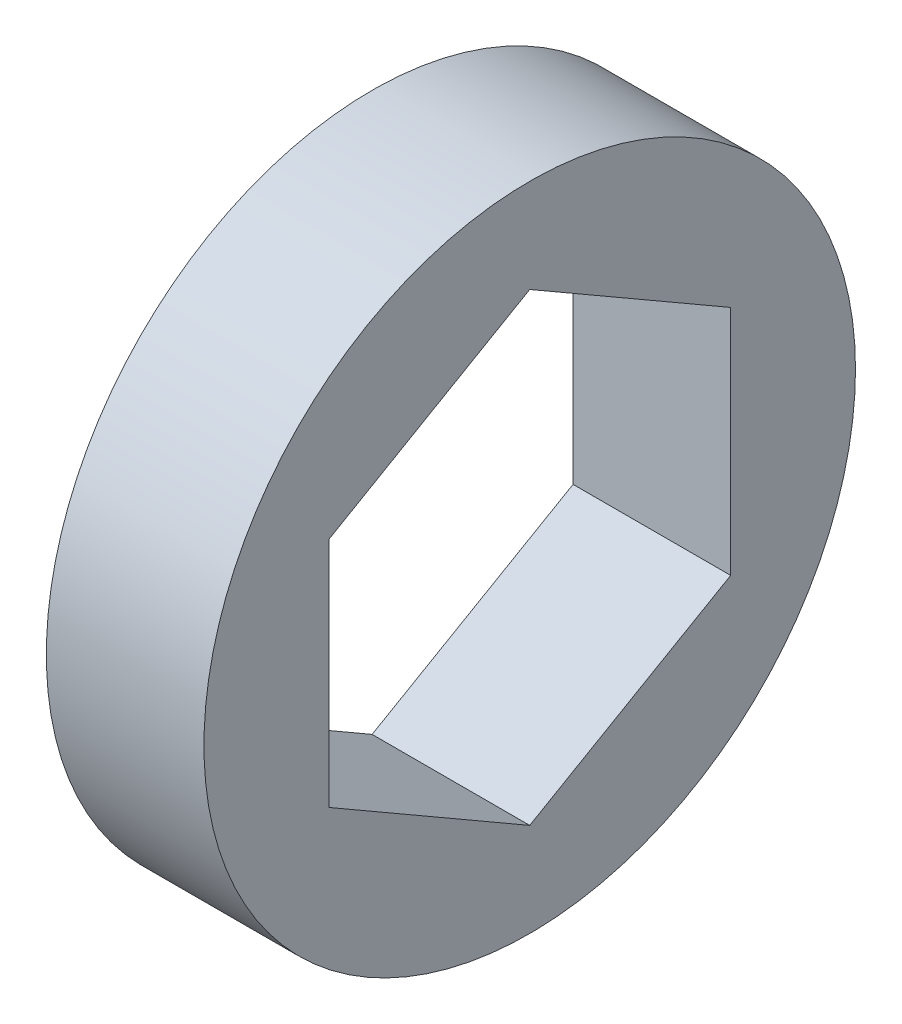
SolidWorks part; units mm, degrees
ref_plane "Front" through (0, 0, 0) normal (0, 0, 1) x (1, 0, 0)
ref_plane "Top" through (0, 0, 0) normal (0, 1, 0) x (1, 0, 0)
ref_plane "Right" through (0, 0, 0) normal (1, 0, 0) x (0, 0, -1)
sketch "Sketch1" plane through (0, 0, 0) normal (1, 0, 0) x (0, 0, -1)
  line L1 (0, 7.479) -> (-6.477, 3.7395)
  line L2 (-6.477, 3.7395) -> (-6.477, -3.7395)
  line L3 (-6.477, -3.7395) -> (0, -7.479)
  line L4 (0, -7.479) -> (6.477, -3.7395)
  line L5 (6.477, -3.7395) -> (6.477, 3.7395)
  line L6 (6.477, 3.7395) -> (0, 7.479)
  circle A0 centre (0, 0) radius 10.5
  circle A1 centre (0, 0) radius 6.477 construction
  dimension "D1" = 21
  dimension "D2" = 12.954
extrude "Boss-Extrude1" add sketch "Sketch1" along normal blind 5.08
